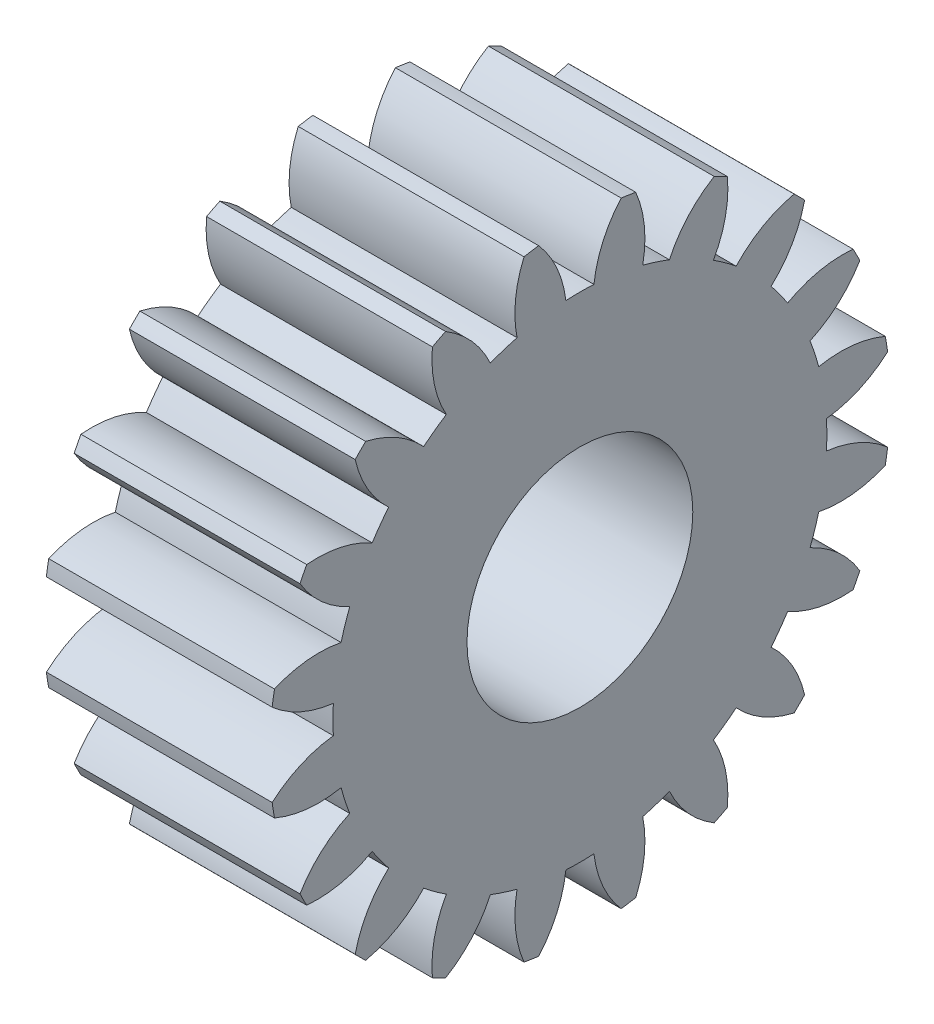
SolidWorks part; units mm, degrees
ref_plane "Plane1" through (0, 0, 0) normal (0, 0, 1) x (1, 0, 0)
ref_plane "Plane2" through (0, 0, 0) normal (0, 1, 0) x (1, 0, 0)
ref_plane "Plane3" through (0, 0, 0) normal (1, 0, 0) x (0, 0, -1)
sketch "HoldingSke" plane through (0, 0, 0) normal (0, 1, 0) x (1, 0, 0)
  line L0 (0, 0) -> (381.8911, -138.997)
  line L1 (-15, 0) -> (100, 0) construction
  line L2 (0, 0) -> (-2.1039, 2.3779)
  line L3 (0, 0) -> (-11.863, 4.5341)
  line L4 (0, 0) -> (8.1152, 2.9537)
  line L5 (0, 0) -> (-47.5972, -17.7524)
  line L6 (0, 0) -> (-10.5278, -7.1032)
  line L7 (-2.1039, 2.3779) -> (8.8308, 51.9871)
  line L8 (-76.2, 54.61) -> (-61.976, 54.61)
  line L9 (-71.009, 38.7566) -> (-53.1078, 45.2721)
  line L10 (-76.2, 71.12) -> (104.1128, 71.12)
  line L11 (0, 0) -> (-12.7, 0)
  line L12 (-76.2, 101.6) -> (-76.1428, 101.6)
  line L13 (24.9733, 27.94) -> (52.9518, 28.4284)
  line L14 (24.9733, 27.94) -> (24.9746, 27.94)
  line L15 (24.9733, 27.94) -> (100.4006, 29.5858)
  circle A0 centre (0, 0) radius 6.35
  circle A1 centre (0, 0) radius 13.8894
  circle A2 centre (0, 0) radius 38.1
  circle A3 centre (0, 0) radius 6.35
  dimension "MHD" = 27.7787
  dimension "Hub_dia" = 76.2
  dimension "Bore" = 12.7
  dimension "MBD" = 12.7
  dimension "Num_teeth" = 20
  dimension "Pitch" = 406.4
  dimension "Overall_len" = 50.8
  dimension "Show_teeth" = 20
  dimension "Thickness" = 12.7
  dimension "OAL" = 50.8001
  dimension "T_dim" = 14.224
  dimension "Ap" = 20
  dimension "H" = 19.05
  dimension "Pitch_radius" = 180.3128
  dimension "Width" = 12.7
  dimension "Backlash" = 0.0571
  dimension "Addendum_fac" = 1
  dimension "Dedendum_fac" = 1.25
  dimension "Clearance_fac" = 0.25
  dimension "Dedendum_add" = 0.0013
sketch "BasProSke" plane through (0, 0, 0) normal (0, 1, 0) x (1, 0, 0)
  line L0 (-10, 0) -> (60, 0) construction
  line L1 (0, 0) -> (0, 17.4625)
  line L2 (0, 0) -> (12.7, 0)
  line L3 (12.7, 0) -> (12.7, 17.4625)
  line L4 (12.7, 17.4625) -> (0, 17.4625)
  dimension "Thickness" = 12.7
  dimension "Diameter" = 34.925
revolve "Base-Revolve" add sketch "BasProSke" angle 360 about L0
sketch "TooCutSke" plane through (0, 0, 0) normal (1, 0, 0) x (0, 0, -1)
  line L1 (0, 0) -> (0, 107) construction
  line L2 (0, 0) -> (-1.3455, 15.8179) construction
  line L3 (0, 0) -> (-4.9538, 31.2774) construction
  line L4 (-1.3455, 15.8179) -> (-2.4769, 15.6387) construction
  arc A0 (0.7888, 13.8669) -> (-0.7888, 13.8669) centre (0, 0) ccw
  arc A1 (2.3397, 17.3307) -> (-2.3397, 17.3307) centre (0, 0) ccw
  circle A2 centre (0, 0) radius 15.875 construction
  circle A3 centre (0, 0) radius 14.9176 construction
  arc A4 (-0.7888, 13.8669) -> (-2.3397, 17.3307) centre (-7.095, 13.1224) ccw
  arc A5 (2.3397, 17.3307) -> (0.7888, 13.8669) centre (7.095, 13.1224) ccw
  dimension "Root_dia" = 27.7787
  dimension "Overcut_dia" = 34.9758
  dimension "Pitch_dia" = 31.75
  dimension "Base_dia" = 29.8352
  dimension "Flank_rad" = 6.35
  dimension "Half_ang" = 9
  dimension "Half_CT" = 1.1455
extrude "ToothCut" cut sketch "TooCutSke" along normal through all
fillet "Breaks" [suppressed] radius 0.0318
fillet "RootFillets" [suppressed] radius 0.3981
pattern_circular "TeethCuts" count 20 every 18 about axis through (-10, 0, 0) along (1, 0, 0) of "ToothCut", "RootFillets", "Breaks"
sketch "HubNeaOneSke" plane through (0, 0, 0) normal (-1, 0, 0) x (0, 0, 1)
  circle A0 centre (0, 0) radius 13.8894
  dimension "Diameter" = 27.7787
extrude "HubNearOne" [suppressed] add sketch "HubNeaOneSke" along normal blind 38.1001
sketch "HubNeaBotSke" plane through (0, 0, 0) normal (-1, 0, 0) x (0, 0, 1)
  circle A0 centre (0, 0) radius 13.8894
  dimension "Diameter" = 27.7787
extrude "HubNearBoth" [suppressed] add sketch "HubNeaBotSke" along normal blind 19.05
ref_plane "FarPln" through (12.7, 0, 0) normal (1, 0, 0) x (0, 0, -1)
sketch "HubFarSke" plane through (12.7, 0, 0) normal (1, 0, 0) x (0, 0, -1)
  circle A0 centre (0, 0) radius 13.8894
  dimension "Diameter" = 27.7787
extrude "HubFar" [suppressed] add sketch "HubFarSke" along normal blind 19.05
sketch "BorSke" plane through (0, 0, 0) normal (1, 0, 0) x (0, 0, -1)
  circle A0 centre (0, 0) radius 6.35
  dimension "Diameter" = 12.7
extrude "Bore" cut sketch "BorSke" along normal mid plane 101.6001
sketch "KeySke" plane through (0, 0, 0) normal (1, 0, 0) x (0, 0, -1)
  line L0 (-1.5875, 0) -> (-1.5875, 7.874)
  line L1 (-1.5875, 7.874) -> (1.5875, 7.874)
  line L2 (1.5875, 7.874) -> (1.5875, 0)
  line L3 (0, 0) -> (0, 34) construction
  line L4 (-1.5875, 0) -> (1.5875, 0)
  dimension "Offset" = 7.874
  dimension "Width" = 3.175
extrude "Keyway" [suppressed] cut sketch "KeySke" along normal mid plane 101.6001
pattern_circular "Keyway2" [suppressed] count 2 every 90 about axis through (-10, 0, 0) along (1, 0, 0)
equation "' \"Pitch@HoldingSke\" = 4"
equation "' \"Num_teeth@HoldingSke\" = 12"
equation "' \"Ap@HoldingSke\" =  20"
equation "' \"Ap@HoldingSke\" = 20"
equation "' \"Width@HoldingSke\" = 0.5"
equation "' \"Hub_dia@HoldingSke\"= 1"
equation "' \"Hub_dia@HoldingSke\" = 1"
equation "' \"Overall_len@HoldingSke\" = 1.0"
equation "' \"Bore@HoldingSke\" = 0.75"
equation "' \"T_dim@HoldingSke\" = 0.85"
equation "' \"Width@KeySke\" = 0.25"
equation "' \"Show_teeth@HoldingSke\" = 13"
equation "' \"Backlash@HoldingSke\" = 0.009"
equation "' \"Addendum_fac@HoldingSke\" = 1.0"
equation "' \"Dedendum_fac@HoldingSke\" = 1.25"
equation "' \"Dedendum_add@HoldingSke\" = 0.00005"
equation "' \"Clearance_fac@HoldingSke\" = 0.25"
equation "' \"Pitch@HoldingSke\" = 0.5"
equation "' \"Num_teeth@HoldingSke\" = 23"
equation "' \"Show_teeth@HoldingSke\" = 23"
equation "' \"Backlash@HoldingSke\" = 0.0375"
equation "\"Overcut_dia@TooCutSke\" = (\"Num_teeth@HoldingSke\" + 2 * \"Addendum_fac@HoldingSke\") / \"Pitch@HoldingSke\" + 0.002"
equation "\"Pitch_dia@TooCutSke\" = \"Num_teeth@HoldingSke\" / \"Pitch@HoldingSke\""
equation "\"Base_dia@TooCutSke\" = \"Num_teeth@HoldingSke\" / \"Pitch@HoldingSke\" * cos((\"Ap@HoldingSke\"  * 3.14159265 / 180))"
equation "\"Root_dia@TooCutSke\" = (\"Num_teeth@HoldingSke\" + 2) / \"Pitch@HoldingSke\" - 2 * (\"Addendum_fac@HoldingSke\" + \"Dedendum_fac@HoldingSke\") / \"Pitch@HoldingSke\" - \"Dedendum_add@HoldingSke\" * 2"
equation "\"Half_ang@TooCutSke\" = 180 / \"Num_teeth@HoldingSke\""
equation "\"Half_CT@TooCutSke\" = \"Num_teeth@HoldingSke\" / \"Pitch@HoldingSke\" * sin((3.14159265 / 2 / \"Num_teeth@HoldingSke\")) / 2 - 7 * \"Backlash@HoldingSke\" / 4"
equation "\"Flank_rad@TooCutSke\" = \"Num_teeth@HoldingSke\" / \"Pitch@HoldingSke\" / 5"
equation "\"Radius@RootFillets\" = \"Clearance_fac@HoldingSke\" / \"Pitch@HoldingSke\" + \"Dedendum_add@HoldingSke\""
equation "\"Break_rad@Breaks\" = 0.02 / \"Pitch@HoldingSke\""
equation "\"Thickness@HoldingSke\" = \"Width@HoldingSke\""
equation "\"OAL@HoldingSke\" = \"Thickness@HoldingSke\""
equation "\"MHD@HoldingSke\" = (\"Num_teeth@HoldingSke\" + 2) / \"Pitch@HoldingSke\" - 2 * (\"Addendum_fac@HoldingSke\" + \"Dedendum_fac@HoldingSke\")  / \"Pitch@HoldingSke\" - \"Dedendum_add@HoldingSke\" * 2"
equation "\"MBD@HoldingSke\" = (\"Num_teeth@HoldingSke\" + 2) / \"Pitch@HoldingSke\" - 2 * (\"Addendum_fac@HoldingSke\" + \"Dedendum_fac@HoldingSke\")  / \"Pitch@HoldingSke\" - \"Dedendum_add@HoldingSke\" * 2 - 0.002"
equation "\"MHD@HoldingSke\" = ((sgn( \"MHD@HoldingSke\" - \"Hub_dia@HoldingSke\" )-1)*( \"MHD@HoldingSke\" - \"Hub_dia@HoldingSke\" ))/-2+ \"Hub_dia@HoldingSke\""
equation "\"MBD@HoldingSke\" = ((sgn( \"MBD@HoldingSke\" - \"Bore@HoldingSke\" )-1)*( \"MBD@HoldingSke\" - \"Bore@HoldingSke\" ))/-2+ \"Bore@HoldingSke\""
equation "\"OAL@HoldingSke\" = ((sgn( \"OAL@HoldingSke\" - \"Overall_len@HoldingSke\" )+1)*( \"OAL@HoldingSke\" - \"Overall_len@HoldingSke\" ))/2 + \"Overall_len@HoldingSke\" + 0.000002"
equation "\"Num_teeth@TeethCuts\" = int( \"Show_teeth@HoldingSke\" ) + 1"
equation "\"Num_teeth@TeethCuts\" = ((sgn( \"Num_teeth@TeethCuts\" - \"Num_teeth@HoldingSke\" )-1)*( \"Num_teeth@TeethCuts\" - \"Num_teeth@HoldingSke\" ))/-2+ \"Num_teeth@HoldingSke\""
equation "\"Num_teeth@TeethCuts\" = ((sgn( \"Num_teeth@TeethCuts\" - 2.0)+1)*( \"Num_teeth@TeethCuts\" - 2.0))/2 +2.0"
equation "\"Angle@TeethCuts\" = 360.0 / \"Num_teeth@HoldingSke\""
equation "\"Diameter@BasProSke\" = (\"Num_teeth@HoldingSke\" + 2 * \"Addendum_fac@HoldingSke\") / \"Pitch@HoldingSke\""
equation "\"Thickness@BasProSke\"  = \"Thickness@HoldingSke\""
equation "' \"Fillet_rad@BasProSke\" =  \"Thickness@HoldingSke\" * 0.05"
equation "' \"Fillet_rad@BasProSke\" = \"Thickness@HoldingSke\" * 0.05"
equation "\"MHD@HoldingSke\" = ((sgn( \"MHD@HoldingSke\" - \"Root_dia@TooCutSke\" )-1)*( \"MHD@HoldingSke\" - \"Root_dia@TooCutSke\" ))/-2+ \"Root_dia@TooCutSke\""
equation "\"Diameter@HubNeaOneSke\" = \"MHD@HoldingSke\""
equation "\"Length@HubNearOne\" = \"OAL@HoldingSke\" - \"Thickness@BasProSke\""
equation "\"Diameter@HubNeaBotSke\" = \"MHD@HoldingSke\""
equation "\"Length@HubNearBoth\" = ( \"OAL@HoldingSke\" - \"Thickness@BasProSke\" ) / 2.0"
equation "\"Thickness@FarPln\" = \"Thickness@BasProSke\""
equation "\"Diameter@HubFarSke\" = \"MHD@HoldingSke\""
equation "\"Length@HubFar\" = ( \"OAL@HoldingSke\" - \"Thickness@BasProSke\" ) / 2.0"
equation "\"Diameter@BorSke\" = \"MBD@HoldingSke\""
equation "\"D1@Bore\" = \"OAL@HoldingSke\" * 2.0"
equation "\"D1@Keyway\" = \"OAL@HoldingSke\" * 2.0"
equation "\"Offset@KeySke\" = \"T_dim@HoldingSke\" - \"MBD@HoldingSke\" / 2.0"
